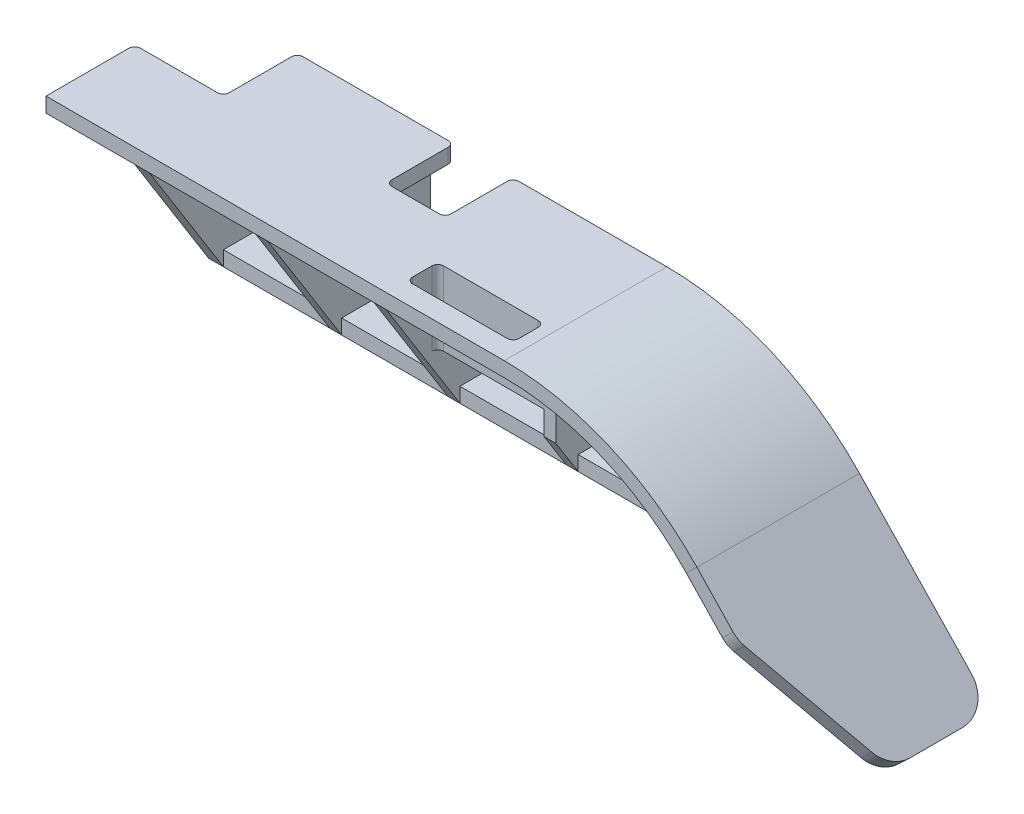
SolidWorks part; units mm, degrees
ref_plane "Front" through (0, 0, 0) normal (0, 0, 1) x (1, 0, 0)
ref_plane "Top" through (0, 0, 0) normal (0, 1, 0) x (1, 0, 0)
ref_plane "Right" through (0, 0, 0) normal (1, 0, 0) x (0, 0, -1)
sketch "Sketch1" plane through (0, 0, 0) normal (0, 1, 0) x (1, 0, 0)
  line L1 (-77.5, 27.5) -> (77.5, 27.5)
  line L2 (-77.5, 27.5) -> (-77.5, -27.5)
  line L3 (-77.5, -27.5) -> (77.5, -27.5)
  line L4 (77.5, 27.5) -> (77.5, -27.5)
  line L5 (-77.5, 27.5) -> (77.5, -27.5) construction
  line L6 (-77.5, -27.5) -> (77.5, 27.5) construction
  point P0 (0, 0)
  dimension "D1" = 155
  dimension "D2" = 55
extrude "Boss-Extrude1" add sketch "Sketch1" along normal blind 5
ref_plane "Plane1" through (0, -40, 0) normal (0, 1, 0) x (1, 0, 0)
sketch "Sketch2" plane through (0, 5, 0) normal (0, 1, 0) x (1, 0, 0)
  line L1 (-77.5, 27.5) -> (-47.5, 27.5)
  line L2 (-77.5, 27.5) -> (-77.5, 2.5)
  line L3 (-77.5, 2.5) -> (-47.5, 2.5)
  line L4 (-47.5, 27.5) -> (-47.5, 2.5)
  dimension "D1" = 25
  dimension "D2" = 30
extrude "Cut-Extrude2" cut sketch "Sketch2" against normal up to surface (5 mm away) up to face at (0, 0, 0)
sketch "Sketch3" plane through (0, 0, 0) normal (0, -1, 0) x (1, 0, 0)
  line L6 (-77.5, 27.5) -> (77.5, 27.5) construction
  line L7 (-47.5, -27.5) -> (-42.5, -27.5)
  line L8 (-47.5, -27.5) -> (-47.5, 27.5)
  line L9 (-47.5, 27.5) -> (-42.5, 27.5)
  line L10 (-42.5, -27.5) -> (-42.5, 27.5)
  dimension "D1" = 5
extrude "Boss-Extrude2" add sketch "Sketch3" along normal up to surface (40 mm away) contours L10 L9 L8 L7 up to plane "Plane1"
sketch "Sketch9" plane through (0, 0, 27.5) normal (0, 0, 1) x (1, 0, 0)
  line L0 (77.5, 5) -> (187.5, 5) construction
  line L1 (187.5, 5) -> (187.5, -70) construction
  line L2 (-77.5, 5) -> (77.5, 5) construction
  line L3 (187.5, -70) -> (142.6724, -22.931)
  line L4 (77.5, 5) -> (77.5, 0) construction
  arc A1 (142.6724, -22.931) -> (77.5, 5) centre (77.5, -85) ccw
  point P12 (141.796, 5)
  dimension "D1" = 110
  dimension "D2" = 75
sketch "Sketch10" plane through (77.5, 0, 0) normal (1, 0, 0) x (0, 0, -1)
  line L0 (-27.5, 5) -> (-27.5, -22.931) construction
  line L1 (27.5, 5) -> (-27.5, 5)
  line L2 (27.5, 5) -> (27.5, 0)
  line L3 (27.5, 0) -> (-27.5, 0)
  line L4 (-27.5, 5) -> (-27.5, 0)
sweep "Sweep1" add profiles "Sketch10" path "Sketch9"
sketch "Sketch14" plane through (0, -40, 0) normal (0, 1, 0) x (1, 0, 0)
  line L1 (-42.5, 27.5) -> (82.5, 27.5)
  line L2 (-42.5, 27.5) -> (-42.5, -2.5)
  line L3 (-42.5, -2.5) -> (82.5, -2.5)
  line L4 (82.5, 27.5) -> (82.5, -2.5)
  dimension "D1" = 125
  dimension "D2" = 30
extrude "Boss-Extrude7" add sketch "Sketch14" along normal blind 5
sketch "Sketch16" plane through (82.5, 0, 0) normal (1, 0, 0) x (0, 0, -1)
  line L1 (27.5, -35) -> (-2.5, -35)
  line L2 (27.5, -35) -> (27.5, -40)
  line L3 (27.5, -40) -> (-2.5, -40)
  line L4 (-2.5, -35) -> (-2.5, -40)
extrude "Boss-Extrude8" add sketch "Sketch16" along normal up to surface (64.7619 mm away)
sketch "Sketch19" plane through (0, 0, 0) normal (0, -1, 0) x (1, 0, 0)
  line L9 (-42.5, 27.5) -> (77.5, 27.5) construction
  line L15 (77.5, -27.5) -> (73.5, -27.5)
  line L16 (77.5, -27.5) -> (77.5, 27.5)
  line L17 (77.5, 27.5) -> (73.5, 27.5)
  line L18 (73.5, -27.5) -> (73.5, 27.5)
  line L19 (37.5, -27.5) -> (37.5, 27.5)
  line L20 (37.5, -27.5) -> (33.5, -27.5)
  line L21 (33.5, -27.5) -> (33.5, 27.5)
  line L22 (37.5, 27.5) -> (33.5, 27.5)
  line L23 (-2.5, -27.5) -> (-2.5, 27.5)
  line L24 (-2.5, -27.5) -> (-6.5, -27.5)
  line L25 (-6.5, -27.5) -> (-6.5, 27.5)
  line L26 (-2.5, 27.5) -> (-6.5, 27.5)
  line L27 (77.5, -27.5) -> (37.5, -27.5) construction
  dimension "D1" = 4
  dimension "D2" = 40
extrude "Boss-Extrude9" add sketch "Sketch19" along normal up to surface (40 mm away) up to face at (20.6746, -40, 0.8333)
sketch "Sketch17" plane through (-47.5, 0, 0) normal (-1, 0, 0) x (0, 0, 1)
  line L0 (27.5, 0) -> (2.5, -40)
  line L1 (2.5, -40) -> (27.5, -40)
  line L2 (27.5, -40) -> (27.5, 0) construction
  line L3 (27.5, -40) -> (27.5, 0)
  line L5 (27.5, -40) -> (-27.5, -40) construction
  dimension "D1" = 0
extrude "Cut-Extrude4" cut sketch "Sketch17" against normal up to surface (125 mm away) up to face at (77.5, -25, 0.8333)
sketch "Sketch18" plane through (0, -35, 0) normal (0, 1, 0) x (1, 0, 0)
  line L0 (-47.5, -2.5) -> (-47.5, 27.5) construction
  line L1 (152.0238, 27.5) -> (-47.5, 27.5) construction
  circle A0 centre (-30.5, 17) radius 1.75
  circle A1 centre (69.5, 17) radius 1.75
  dimension "D1" = 3.5
  dimension "D2" = 17
  dimension "D3" = 100
  dimension "D4" = 10.5
extrude "Cut-Extrude5" cut sketch "Sketch18" against normal up to surface (5 mm away) up to face at (34.5043, -40, -2.9545)
sketch "Sketch20" plane through (0, -35, 0) normal (0, 1, 0) x (1, 0, 0)
  line L0 (77.5, 27.5) -> (77.5, -2.5) construction
  line L1 (81.5, 1.5) -> (119.5, 1.5)
  line L2 (81.5, 1.5) -> (81.5, 17.5)
  line L3 (81.5, 17.5) -> (119.5, 17.5)
  line L4 (119.5, 1.5) -> (119.5, 17.5)
  line L5 (77.5, -2.5) -> (147.2619, -2.5) construction
  dimension "D1" = 16
  dimension "D2" = 4
  dimension "D3" = 4
  dimension "D4" = 38
extrude "Cut-Extrude6" cut sketch "Sketch20" against normal up to surface (5 mm away) up to face at (-30.5, -40, -15.25)
fillet "Fillet1" radius 5 4 edges at (119.5, -37.5, -17.5) (119.5, -37.5, -1.5) (81.5, -37.5, -1.5) (81.5, -37.5, -17.5)
sketch "Sketch21" plane through (73.5, 0, 0) normal (-1, 0, 0) x (0, 0, 1)
  line L6 (27.5, 0) -> (-27.5, 0) construction
  line L11 (10, 0) -> (5, 0)
  line L12 (10, 0) -> (10, -20)
  line L13 (10, -20) -> (5, -20)
  line L14 (5, 0) -> (5, -20)
  dimension "D1" = 5
  dimension "D2" = 17.5
  dimension "D3" = 20
extrude "Boss-Extrude10" add sketch "Sketch21" along normal up to surface (36 mm away) up to face at (37.5, -22, -4.5)
sketch "Sketch22" plane through (73.5, 0, 0) normal (-1, 0, 0) x (0, 0, 1)
  line L2 (10, -28) -> (27.5, 0)
  line L3 (27.5, 0) -> (10, 0)
  line L4 (10, 0) -> (10, -28)
  line L5 (2.5, -40) -> (27.5, 0) construction
extrude "Cut-Extrude7" cut sketch "Sketch22" against normal up to surface (4 mm away) up to face at (77.5, -22, -4.5)
sketch "Sketch23" plane through (0, 0, 0) normal (0, -1, 0) x (1, 0, 0)
  line L7 (37.5, 10) -> (73.5, 10)
  line L8 (37.5, 10) -> (37.5, 20.5)
  line L9 (37.5, 20.5) -> (73.5, 20.5)
  line L10 (73.5, 10) -> (73.5, 20.5)
  line L14 (37.5, 10) -> (73.5, 10) construction
  line L15 (77.5, 27.5) -> (77.5, 10) construction
  line L16 (37.5, 10) -> (37.5, 27.5) construction
  dimension "D1" = 10.5
  dimension "D2" = 4
extrude "Cut-Extrude8" cut sketch "Sketch23" against normal up to surface (5 mm away) up to face at (-15.8333, 5, -0.8333)
fillet "Fillet2" radius 2 4 edges at (73.5, 2.5, 20.5) (73.5, 2.5, 10) (37.5, 2.5, 20.5) (37.5, -7.5, 10)
sketch "Sketch24" plane through (0, 0, 0) normal (0, -1, 0) x (1, 0, 0)
  line L0 (33.5, -27.5) -> (-2.5, -27.5) construction
  line L1 (25.5, -27.5) -> (5.5, -27.5)
  line L2 (25.5, -27.5) -> (25.5, -4.5)
  line L3 (25.5, -4.5) -> (5.5, -4.5)
  line L4 (5.5, -27.5) -> (5.5, -4.5)
  line L5 (-47.5, -2.5) -> (-47.5, -27.5) construction
  dimension "D1" = 20
  dimension "D2" = 53
  dimension "D3" = 23
extrude "Cut-Extrude9" cut sketch "Sketch24" against normal up to surface (5 mm away) up to face at (55.5, 5, 15.25)
fillet "Fillet3" radius 2 7 edges at (-47.5, 2.5, -2.5) (5.5, 2.5, -4.5) (5.5, 2.5, -27.5) (25.5, 2.5, -4.5) (25.5, 2.5, -27.5) (-47.5, -17.5, -27.5) (-77.5, 2.5, -2.5)
chamfer "Chamfer1" distance 45 angle 25 1 edges at (185.6897, -71.7241, 27.5)
fillet "Fillet4" radius 10 2 edges at (154.6552, -39.1379, 27.5) (185.6897, -71.7241, 6.5162)
fillet "Fillet5" radius 10 1 edges at (185.6897, -71.7241, -27.5)
